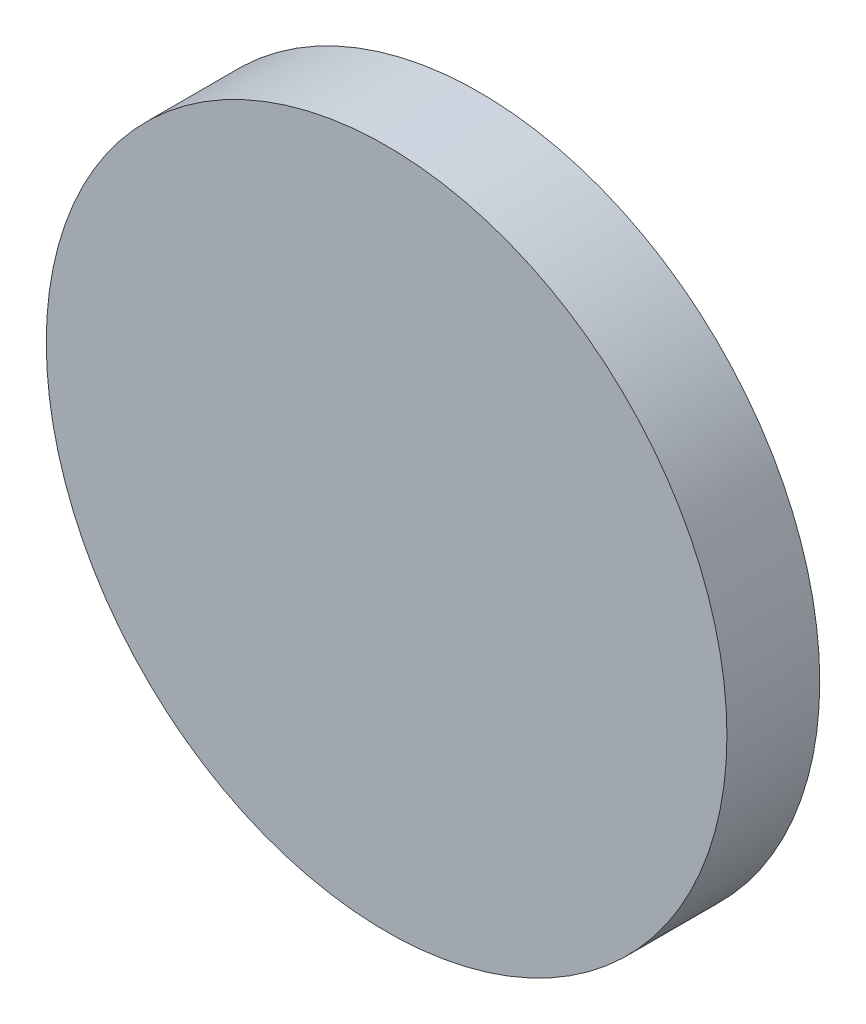
SolidWorks part; units mm, degrees
ref_plane "Front Plane" through (0, 0, 0) normal (0, 0, 1) x (1, 0, 0)
ref_plane "Top Plane" through (0, 0, 0) normal (0, 1, 0) x (1, 0, 0)
ref_plane "Right Plane" through (0, 0, 0) normal (1, 0, 0) x (0, 0, -1)
sketch "Sketch1" plane through (0, 0, 0) normal (0, 0, 1) x (1, 0, 0)
  circle A0 centre (0, 0) radius 9.3142
extrude "Boss-Extrude1" add sketch "Sketch1" along normal blind 2.54
